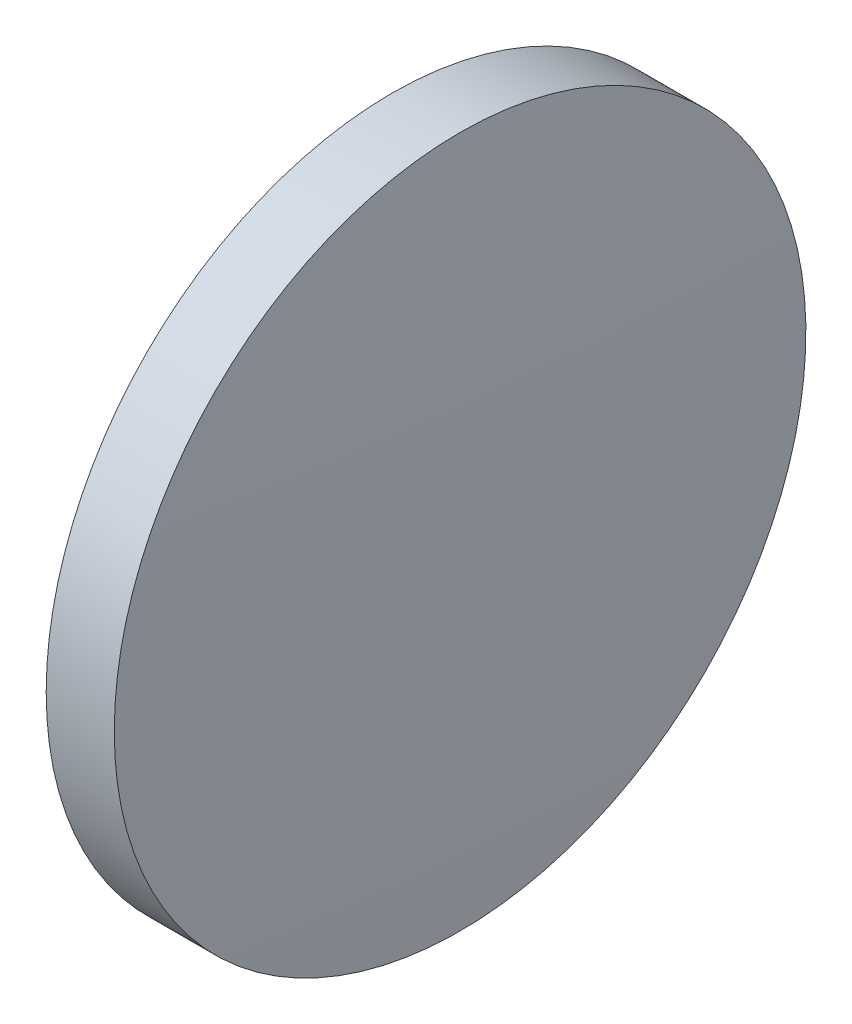
SolidWorks part; units mm, degrees
ref_plane "前视基准面" through (0, 0, 0) normal (0, 0, 1) x (1, 0, 0)
ref_plane "上视基准面" through (0, 0, 0) normal (0, 1, 0) x (1, 0, 0)
ref_plane "右视基准面" through (0, 0, 0) normal (1, 0, 0) x (0, 0, -1)
sketch "草图1" plane through (0, 0, 0) normal (0, 0, 1) x (1, 0, 0)
  line L0 (83.372, 48.6161) -> (89.8656, 48.6161) construction
  line L1 (85.2082, 61.3161) -> (87.7082, 61.3161)
  line L2 (87.7082, 61.3161) -> (87.7082, 35.9161)
  line L3 (87.7082, 35.9161) -> (85.2082, 35.9161)
  line L4 (85.2082, 35.9161) -> (85.2082, 61.3161)
  arc A0 (85.2082, 61.3161) -> (85.2082, 35.9161) centre (358.4721, 48.6161) ccw
  arc A1 (87.7082, 35.9161) -> (87.7082, 61.3161) centre (-185.5557, 48.6161) ccw
  dimension "D1" = 25.4
  dimension "D2" = 2.5
revolve "旋转1" add sketch "草图1" angle 360 about L0
